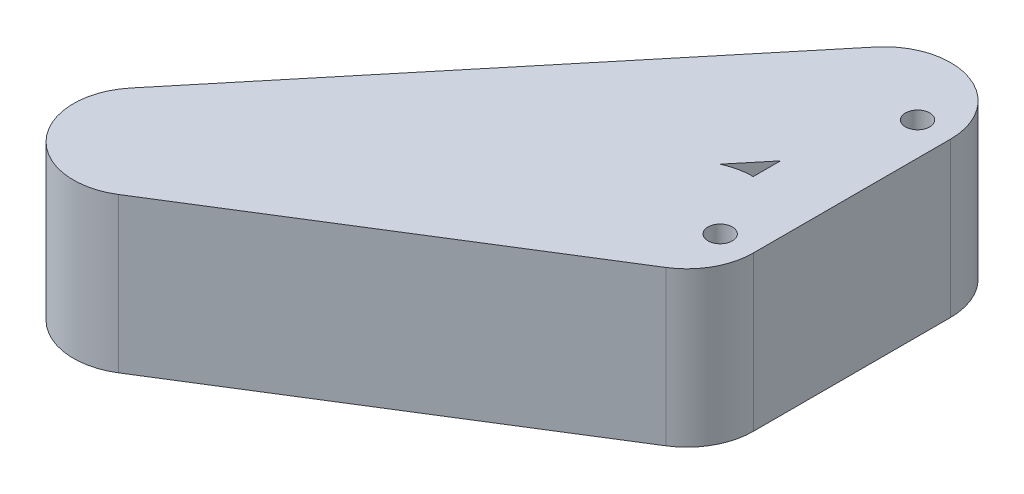
SolidWorks part; units mm, degrees
ref_plane "Front Plane" through (0, 0, 0) normal (0, 0, 1) x (1, 0, 0)
ref_plane "Top Plane" through (0, 0, 0) normal (0, 1, 0) x (1, 0, 0)
ref_plane "Right Plane" through (0, 0, 0) normal (1, 0, 0) x (0, 0, -1)
sketch "Sketch1" plane through (0, 0, 0) normal (0, 1, 0) x (1, 0, 0)
  line L0 (0, 0) -> (0, 44.72)
  line L1 (0, 44.72) -> (0, 0) construction
  line L2 (7.5, 44.72) -> (7.5, 0)
  line L3 (-7.5, 44.72) -> (-7.5, 0)
  circle A0 centre (0, 44.72) radius 2.75
  circle A1 centre (0, 0) radius 2.75
  arc A2 (7.5, 44.72) -> (-7.5, 44.72) centre (0, 44.72) ccw
  arc A3 (-7.5, 0) -> (7.5, 0) centre (0, 0) ccw
  point P5 (0, 22.36)
extrude "Boss-Extrude1" add sketch "Sketch1" along normal blind 35
sketch "Sketch2" plane through (0, 0, 0) normal (0, -1, 0) x (1, 0, 0)
  line L0 (-7.5, 0) -> (-83.8243, 47.6927)
  line L1 (-83.8243, 47.6927) -> (-7.5, -44.72)
  line L2 (-83.8243, 47.6927) -> (-7.5, 0) construction
  line L3 (-75.8755, 60.4135) -> (0.4488, 12.7207)
  line L4 (-91.7731, 34.972) -> (-15.4488, -12.7207)
  line L5 (-83.8243, 47.6927) -> (-7.5, -44.72) construction
  line L6 (-72.2589, 57.2447) -> (4.0654, -35.168)
  line L7 (-95.3898, 38.1407) -> (-19.0654, -54.272)
  arc A0 (-75.8755, 60.4135) -> (-91.7731, 34.972) centre (-83.8243, 47.6927) ccw
  arc A1 (-15.4488, -12.7207) -> (0.4488, 12.7207) centre (-7.5, 0) ccw
  arc A2 (-72.2589, 57.2447) -> (-95.3898, 38.1407) centre (-83.8243, 47.6927) ccw
  arc A3 (-19.0654, -54.272) -> (4.0654, -35.168) centre (-7.5, -44.72) ccw
  circle A4 centre (0, -44.72) radius 2.75
  circle A5 centre (0, 0) radius 2.75
  point P3 (-45.6622, 23.8464)
  point P11 (-45.6622, 1.4864)
  circle M2 centre (0, -44.72) radius 2.75
  circle M3 centre (0, 0) radius 2.75
  line M4 (-7.5, 0) -> (-7.5, -44.72)
  arc M5 (-7.5, -44.72) -> (7.5, -44.72) centre (0, -44.72) ccw
  arc M7 (7.5, 0) -> (-7.5, 0) centre (0, 0) ccw
extrude "Boss-Extrude2" add sketch "Sketch2" against normal blind 35 contours L7 A3 L1 L4 A0 M5 | A1 L4 L1 L6 M4 | A3 L6 M5 M4 M2 | L4 A1 L6 L0 L1 | L6 A2 A0 L4 L1 L0 | A2 L6 L0 A1 L3 M7 | L6 A1 L0 M4 | A1 M4 M7 M3
